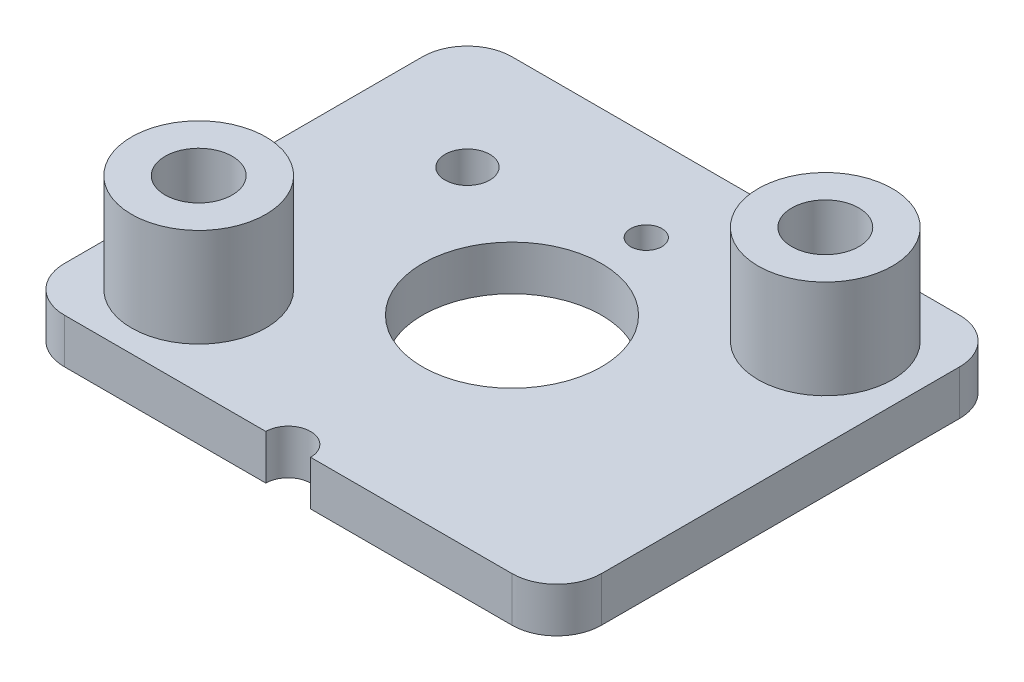
SolidWorks part; units mm, degrees
ref_plane "Alzado" through (0, 0, 0) normal (0, 0, 1) x (1, 0, 0)
ref_plane "Planta" through (0, 0, 0) normal (0, 1, 0) x (1, 0, 0)
ref_plane "Vista lateral" through (0, 0, 0) normal (1, 0, 0) x (0, 0, -1)
sketch "Croquis1" plane through (0, 0, 0) normal (0, 1, 0) x (1, 0, 0)
  line L0 (0, 0) -> (0, 6.7969) construction
  line L1 (-6, 5) -> (6, 5)
  line L2 (-6, 5) -> (-6, -5)
  line L3 (-6, -5) -> (-0.5, -5)
  line L4 (6, 5) -> (6, -5)
  line L5 (0.5, -5) -> (6, -5)
  line L7 (0, 0) -> (6.6455, 0) construction
  circle A0 centre (4, 3) radius 1.5
  circle A2 centre (-4, -3) radius 1.5
  circle A3 centre (0, 0) radius 2
  circle A4 centre (0, 3) radius 0.35
  circle A5 centre (-3.3606, 2.3649) radius 0.5
  arc A6 (-0.5, -5) -> (0.5, -5) centre (0, -5) cw
  dimension "D3" = 3
  dimension "D6" = 4
  dimension "D7" = 0.7
  dimension "D11" = 1
  dimension "D1" = 10
  dimension "D2" = 12
  dimension "D4" = 2
  dimension "D5" = 2
  dimension "D8" = 2
extrude "Saliente-Extruir1" add sketch "Croquis1" along normal blind 1
sketch "Croquis2" plane through (0, 1, 0) normal (0, 1, 0) x (1, 0, 0)
  circle A0 centre (4, 3) radius 1.5
  circle A1 centre (-4, -3) radius 1.5
extrude "Saliente-Extruir2" add sketch "Croquis2" along normal blind 2.2 separate body
fillet "Redondeo1" radius 1 4 edges at (-6, 0.5, 5) (6, 0.5, -5) (-6, 0.5, -5) (6, 0.5, 5)
sketch "Croquis3" plane through (0, 3.2, 0) normal (0, 1, 0) x (1, 0, 0)
  circle A0 centre (4, 3) radius 0.75
  circle A1 centre (-4, -3) radius 0.75
  dimension "D1" = 1.5
  dimension "D2" = 1.5
extrude "Cortar-Extruir1" cut sketch "Croquis3" against normal blind 2.2
